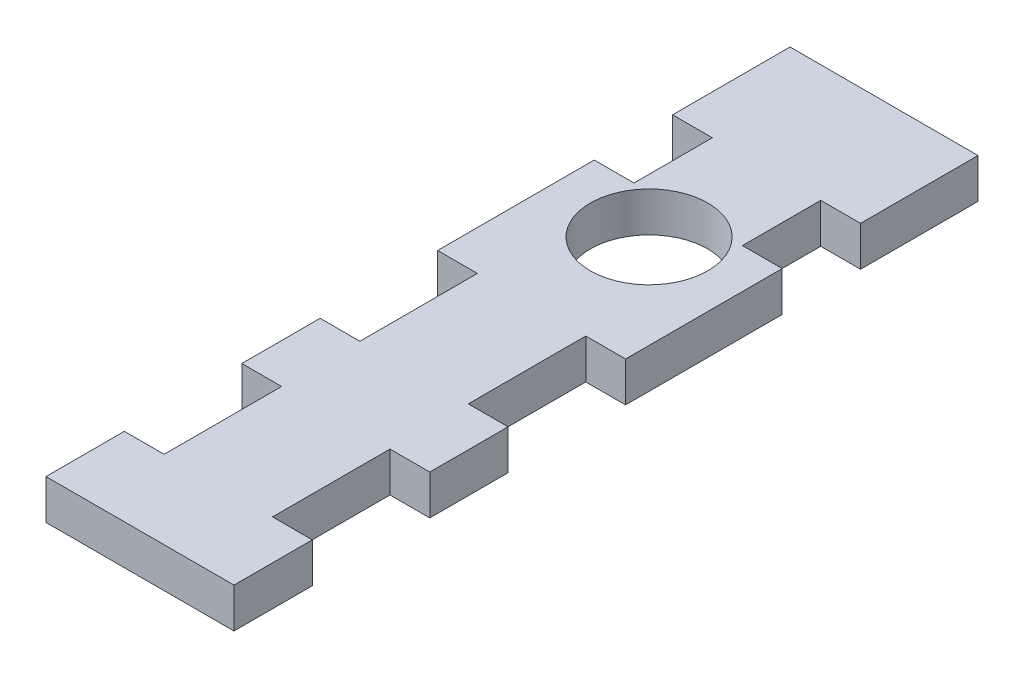
SolidWorks part; units mm, degrees
ref_plane "Front Plane" through (0, 0, 0) normal (0, 0, 1) x (1, 0, 0)
ref_plane "Top Plane" through (0, 0, 0) normal (0, 1, 0) x (1, 0, 0)
ref_plane "Right Plane" through (0, 0, 0) normal (1, 0, 0) x (0, 0, -1)
sketch "Sketch1" plane through (0, 0, 0) normal (0, 1, 0) x (1, 0, 0)
  line L0 (-12, 32.5) -> (12, 32.5) construction
  line L1 (12, -32.5) -> (-12, -32.5)
  line L2 (12, -32.5) -> (12, 32.5)
  line L3 (12, 32.5) -> (12, 62.5)
  line L4 (-12, -32.5) -> (-12, 32.5)
  line L5 (12, -32.5) -> (-12, 32.5) construction
  line L6 (12, 32.5) -> (-12, -32.5) construction
  line L7 (12, 62.5) -> (-12, 62.5)
  line L8 (-12, 62.5) -> (-12, 32.5)
  circle A1 centre (0, 32.5) radius 7.5
  point P0 (0, 0)
  dimension "D3" = 15
  dimension "D4" = 30
  dimension "D1" = 65
  dimension "D2" = 24
extrude "Boss-Extrude1" add sketch "Sketch1" along normal blind 5.08
sketch "Sketch2" plane through (0, 5.08, 0) normal (0, 1, 0) x (1, 0, 0)
  line L0 (-12, -32.5) -> (12, -32.5) construction
  line L1 (-12, 62.5) -> (-12, -32.5) construction
  line L2 (-12, 62.5) -> (-12, -32.5) construction
  line L3 (-12, 37.5) -> (-6.92, 37.5)
  line L4 (-12, 37.5) -> (-12, 47.5)
  line L5 (-12, 47.5) -> (-6.92, 47.5)
  line L6 (-6.92, 37.5) -> (-6.92, 47.5)
  line L15 (-12, -22.5) -> (-6.92, -22.5)
  line L16 (-12, -22.5) -> (-12, -7.5)
  line L17 (-12, -7.5) -> (-6.92, -7.5)
  line L18 (-6.92, -22.5) -> (-6.92, -7.5)
  line L19 (-12, 2.5) -> (-6.92, 2.5)
  line L20 (-12, 2.5) -> (-12, 17.5)
  line L21 (-12, 17.5) -> (-6.92, 17.5)
  line L22 (-6.92, 2.5) -> (-6.92, 17.5)
  dimension "D1" = 15
  dimension "D2" = 10
  dimension "D4" = 5.08
  dimension "D3" = 10
  dimension "D5" = 20
  dimension "D6" = 10
extrude "Cut-Extrude1" cut sketch "Sketch2" against normal up to surface (5.08 mm away) up to face at (0, 0, -15)
mirror "Mirror2" about plane through (0, 0, 0) normal (1, 0, 0) of "Cut-Extrude1"
